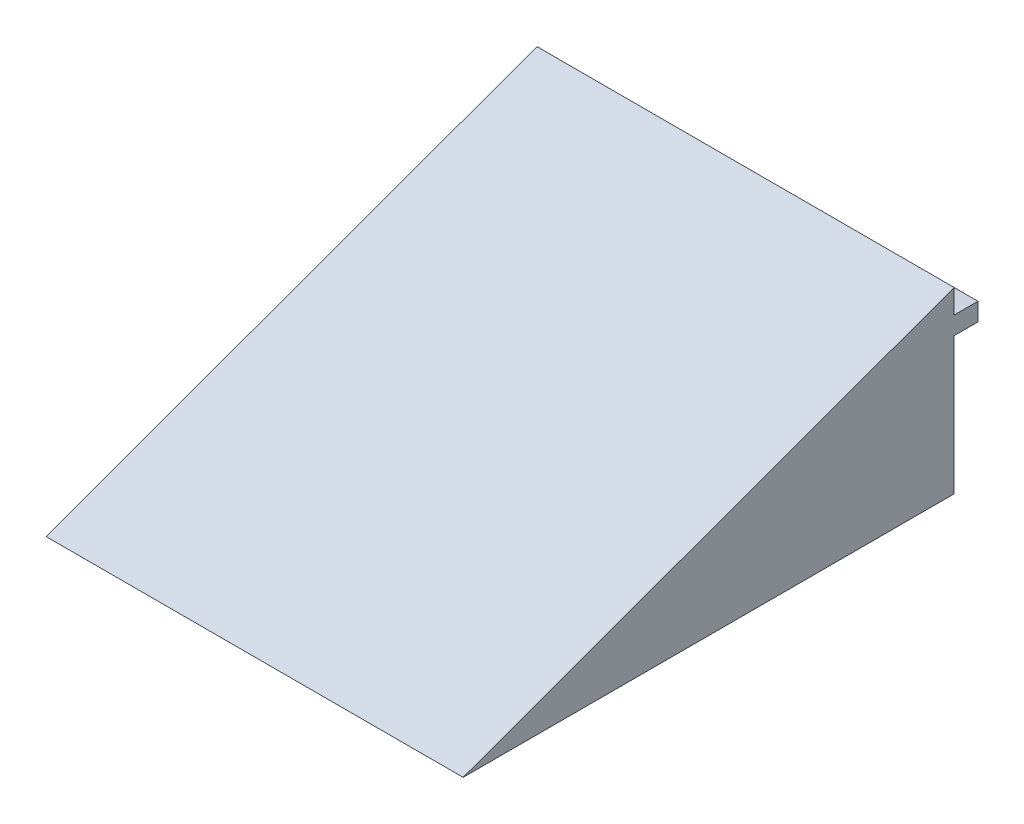
SolidWorks part; units mm, degrees
ref_plane "Front Plane" through (0, 0, 0) normal (0, 0, 1) x (1, 0, 0)
ref_plane "Top Plane" through (0, 0, 0) normal (0, 1, 0) x (1, 0, 0)
ref_plane "Right Plane" through (0, 0, 0) normal (1, 0, 0) x (0, 0, -1)
sketch "Sketch1" plane through (0, 0, 0) normal (1, 0, 0) x (0, 0, -1)
  line L0 (0, 0) -> (412, 0)
  line L1 (412, 0) -> (412, 149.9557)
  line L2 (412, 149.9557) -> (0, 0)
  dimension "D1" = 412
  dimension "D2" = 20
extrude "Boss-Extrude1" add sketch "Sketch1" against normal blind 350
sketch "Sketch3" plane through (0, 0, -412) normal (0, 0, -1) x (-1, 0, 0)
  line L0 (0, 0) -> (0, 149.9557) construction
  line L1 (0, 129.9557) -> (350, 129.9557)
  line L2 (0, 129.9557) -> (0, 114.9557)
  line L3 (0, 114.9557) -> (350, 114.9557)
  line L4 (350, 129.9557) -> (350, 114.9557)
  line L5 (350, 0) -> (350, 149.9557) construction
  line L6 (350, 149.9557) -> (0, 149.9557) construction
  dimension "D1" = 15
  dimension "D2" = 20
extrude "Boss-Extrude2" add sketch "Sketch3" along normal blind 20
